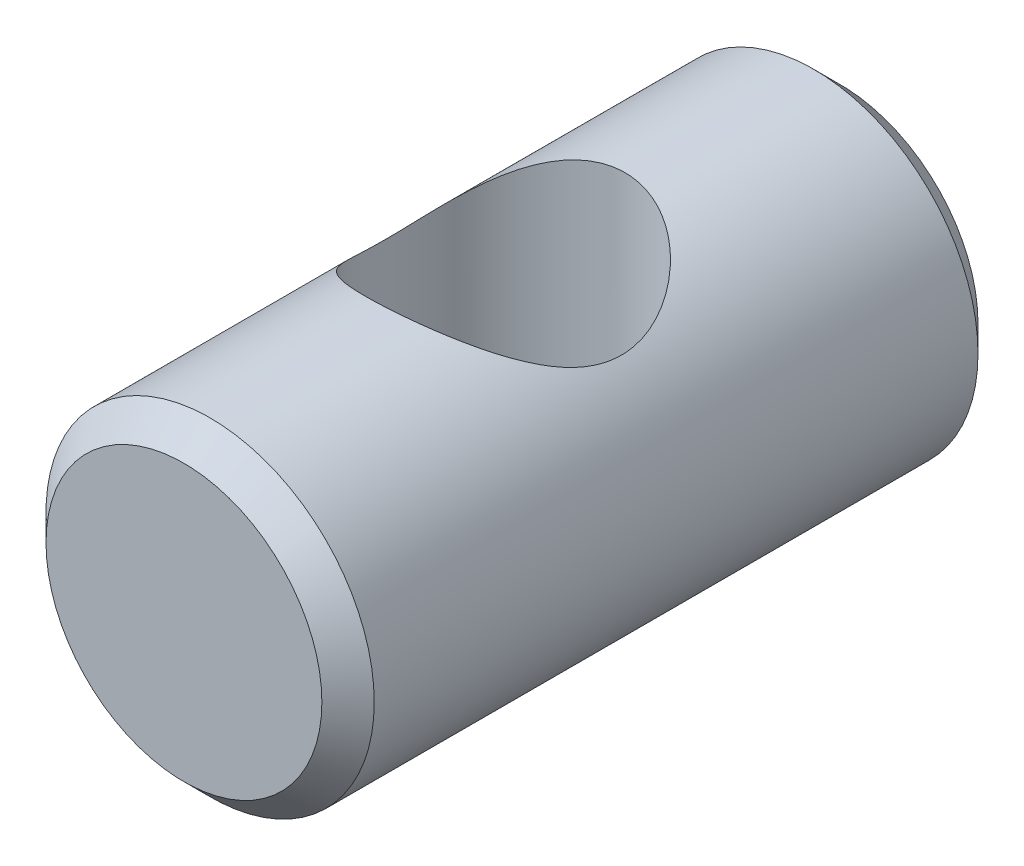
SolidWorks part; units mm, degrees
ref_plane "Front Plane" through (0, 0, 0) normal (0, 0, 1) x (1, 0, 0)
ref_plane "Top Plane" through (0, 0, 0) normal (0, 1, 0) x (1, 0, 0)
ref_plane "Right Plane" through (0, 0, 0) normal (1, 0, 0) x (0, 0, -1)
sketch "Sketch2" plane through (0, 0, 0) normal (0, 0, 1) x (1, 0, 0)
  circle A0 centre (0, 0) radius 4.765
  dimension "D1" = 9.53
extrude "Boss-Extrude1" add sketch "Sketch2" along normal mid plane 19.05
chamfer "Chamfer1" distance 0.76 angle 45 2 edges at (4.765, 0, -9.525) (4.765, 0, 9.525)
sketch "Sketch3" plane through (0, 0, 0) normal (0, 1, 0) x (1, 0, 0)
  circle A0 centre (-0.25, 0) radius 3.43
  point P2 (0, 0)
  dimension "D1" = 6.86
  dimension "D2" = 0.25
extrude "Cut-Extrude1" cut sketch "Sketch3" against normal through all both and the other way through all
